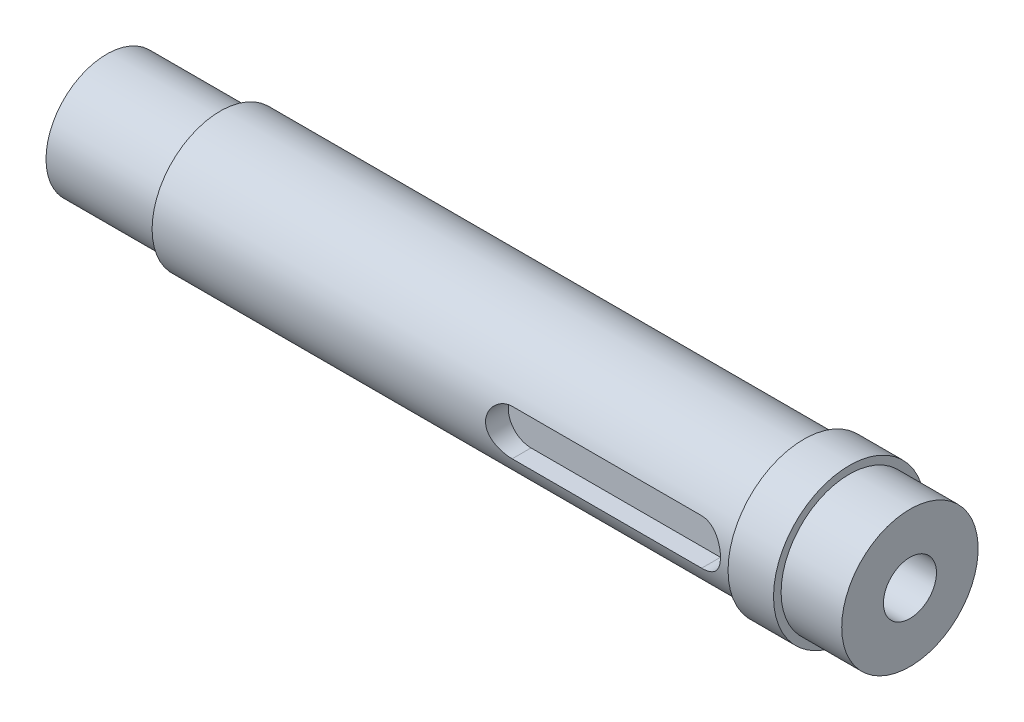
SolidWorks part; units mm, degrees
material "普通碳钢"
ref_plane "前视基准面" through (0, 0, 0) normal (0, 0, 1) x (1, 0, 0)
ref_plane "上视基准面" through (0, 0, 0) normal (0, 1, 0) x (1, 0, 0)
ref_plane "右视基准面" through (0, 0, 0) normal (1, 0, 0) x (0, 0, -1)
sketch "草图2" plane through (0, 0, 0) normal (0, 1, 0) x (1, 0, 0)
  line L0 (0, 0) -> (165.8153, 0) construction
  line L1 (0, 0) -> (0, 8)
  line L2 (15, 9) -> (92, 9)
  line L3 (92, 9) -> (92, 10)
  line L4 (92, 10) -> (98, 10)
  line L5 (15, 9) -> (15, 8)
  line L6 (15, 8) -> (0, 8)
  line L7 (98, 10) -> (98, 9)
  line L8 (98, 9) -> (106, 9)
  line L11 (106, 9) -> (106, 0)
  line L12 (0, 0) -> (106, 0)
  dimension "D1" = 106
  dimension "D2" = 8
  dimension "D3" = 15
  dimension "D4" = 77
  dimension "D5" = 9
  dimension "D6" = 10
  dimension "D7" = 9
  dimension "D8" = 8
  dimension "D9" = 6
revolve "旋转1" add sketch "草图2" angle 360 about L0
cosmetic thread "装饰螺纹线1" parameters "D1"=13, "D2"=13.835
ref_plane "基准面1" through (0, 0, 9) normal (0, 0, 1) x (1, 0, 0)
sketch "草图4" plane through (0, 0, 9) normal (0, 0, 1) x (1, 0, 0)
  line L0 (0, 0) -> (48.9051, 0) construction
  line L1 (62, 0) -> (87, 0) construction
  line L2 (62, 3) -> (87, 3)
  line L3 (62, -3) -> (87, -3)
  line L4 (92, 9) -> (92, -9) construction
  arc A0 (62, 3) -> (62, -3) centre (62, 0) ccw
  arc A1 (87, -3) -> (87, 3) centre (87, 0) ccw
  point P5 (74.5, 0)
  dimension "D1" = 3
  dimension "D2" = 25
  dimension "D3" = 5
extrude "切除-拉伸2" cut sketch "草图4" against normal blind 3
sketch "草图5" plane through (106, 0, 0) normal (1, 0, 0) x (0, 0, -1)
  circle A0 centre (0, 0) radius 3.5
  dimension "D1" = 7
extrude "切除-拉伸3" cut sketch "草图5" against normal through all
equation "\"16。5\"=23.2"
